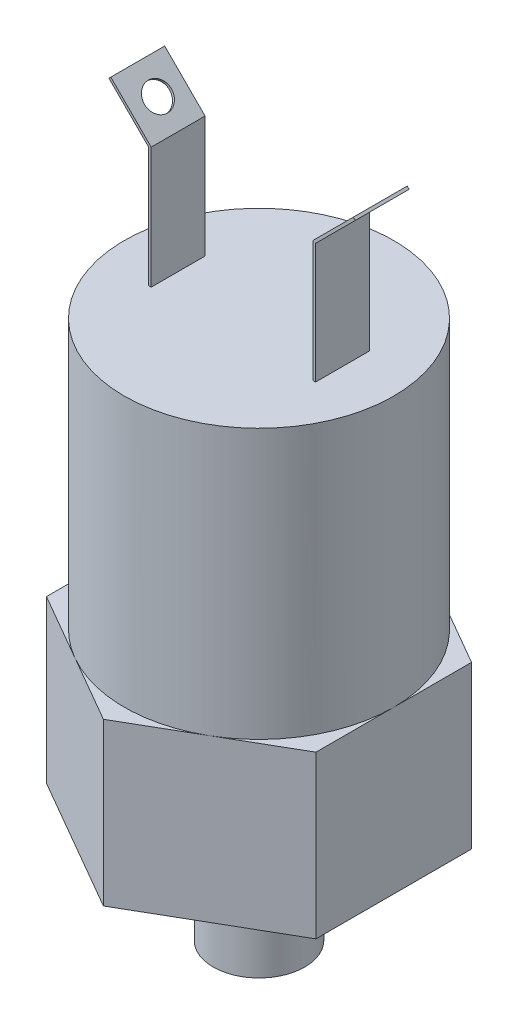
SolidWorks part; units mm, degrees
ref_plane "Front Plane" through (0, 0, 0) normal (0, 0, 1) x (1, 0, 0)
ref_plane "Top Plane" through (0, 0, 0) normal (0, 1, 0) x (1, 0, 0)
ref_plane "Right Plane" through (0, 0, 0) normal (1, 0, 0) x (0, 0, -1)
sketch "Sketch1" plane through (0, 0, 0) normal (0, 1, 0) x (1, 0, 0)
  circle A0 centre (0, 0) radius 4.318
  dimension "D1" = 8.636
extrude "Boss-Extrude1" add sketch "Sketch1" along normal blind 10.16
cosmetic thread "Cosmetic Thread1" parameters "D2"=7.636
sketch "Sketch2" plane through (0, 10.16, 0) normal (0, 1, 0) x (1, 0, 0)
  line L1 (0, 14.6647) -> (-12.7, 7.3323)
  line L2 (-12.7, 7.3323) -> (-12.7, -7.3323)
  line L3 (-12.7, -7.3323) -> (0, -14.6647)
  line L4 (0, -14.6647) -> (12.7, -7.3323)
  line L5 (12.7, -7.3323) -> (12.7, 7.3323)
  line L6 (12.7, 7.3323) -> (0, 14.6647)
  circle A0 centre (0, 0) radius 12.7 construction
  dimension "D1" = 25.4
extrude "Boss-Extrude2" add sketch "Sketch2" along normal blind 15.24
sketch "Sketch3" plane through (0, 25.4, 0) normal (0, 1, 0) x (1, 0, 0)
  circle A0 centre (0, 0) radius 12.7
  dimension "D1" = 25.4
extrude "Boss-Extrude3" add sketch "Sketch3" along normal blind 25.4
sketch "Sketch4" plane through (0, 0, 0) normal (0, 0, 1) x (1, 0, 0)
  line L0 (7.62, 50.8) -> (7.62, 62.23)
  line L1 (12.7, 50.8) -> (-12.7, 50.8) construction
  line L2 (7.62, 62.23) -> (11.43, 66.04)
  line L3 (12.7, 25.4) -> (12.7, 50.8) construction
  dimension "D1" = 15.24
  dimension "D2" = 45
  dimension "D3" = 11.43
  dimension "D4" = 5.08
extrude "Extrude-Thin1" add sketch "Sketch4" along normal mid plane 5.08 thin
sketch "Sketch5" plane through (-27.305, 27.305, 0) normal (-0.7071, 0.7071, 0) x (0, 0, 1)
  line L0 (-2.54, 54.7796) -> (2.54, 49.3914) construction
  line L1 (2.54, 54.7796) -> (-2.54, 49.3914) construction
  circle A0 centre (0, 52.0855) radius 1.27
  dimension "D1" = 2.54
extrude "Cut-Extrude1" cut sketch "Sketch5" against normal up to next (0.254 mm away)
mirror "Mirror1" about plane through (0, 0, 0) normal (1, 0, 0) of "Cut-Extrude1", "Extrude-Thin1"
